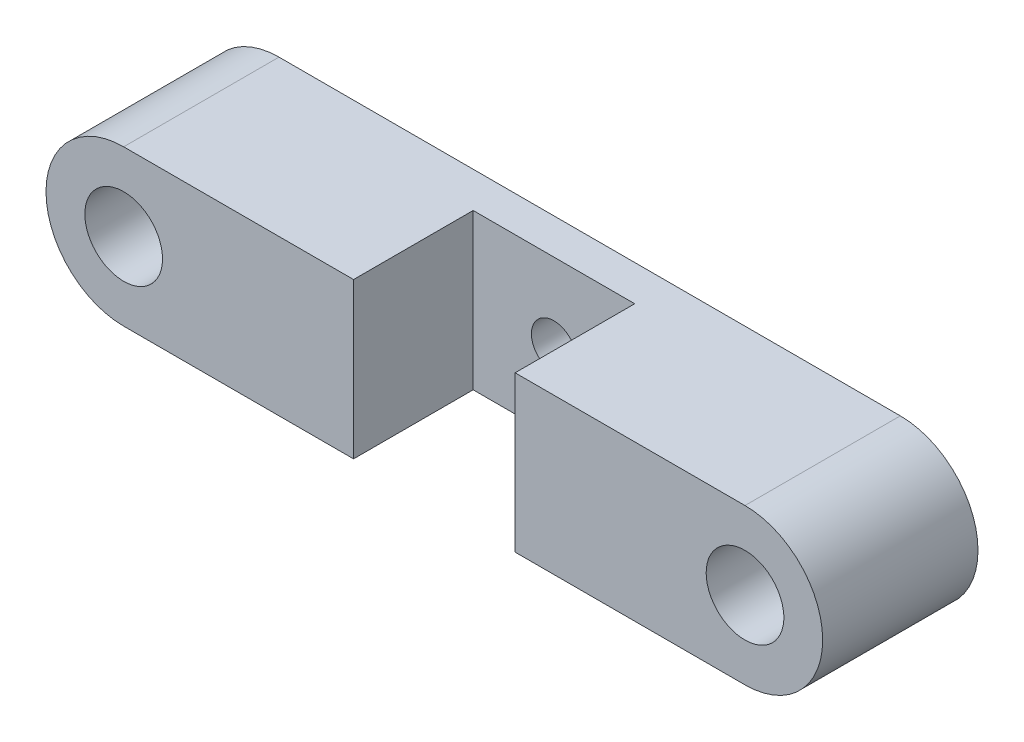
SolidWorks part; units mm, degrees
material "ABS"
ref_plane "Front Plane" through (0, 0, 0) normal (0, 0, 1) x (1, 0, 0)
ref_plane "Top Plane" through (0, 0, 0) normal (0, 1, 0) x (1, 0, 0)
ref_plane "Right Plane" through (0, 0, 0) normal (1, 0, 0) x (0, 0, -1)
sketch "Sketch1" plane through (0, 0, 0) normal (0, 0, 1) x (1, 0, 0)
  line L0 (-50.8, 0) -> (50.8, 0) construction
  line L1 (-50.8, 12.7) -> (50.8, 12.7)
  line L2 (-50.8, -12.7) -> (50.8, -12.7)
  line L3 (0, 34.5997) -> (0, -36.6368) construction
  arc A0 (-50.8, 12.7) -> (-50.8, -12.7) centre (-50.8, 0) ccw
  arc A1 (50.8, -12.7) -> (50.8, 12.7) centre (50.8, 0) ccw
  circle A2 centre (-50.8, 0) radius 6.35
  circle A3 centre (50.8, 0) radius 6.35
  point P3 (0, 0)
  dimension "D3" = 12.7
  dimension "D1" = 101.6
  dimension "D2" = 25.4
extrude "Boss-Extrude1" add sketch "Sketch1" along normal blind 25.4
sketch "Sketch2" plane through (0, 12.7, 0) normal (0, 1, 0) x (1, 0, 0)
  line L0 (50.8, -25.4) -> (-50.8, -25.4) construction
  line L1 (-12.7, -6.35) -> (12.7, -6.35) construction
  line L2 (-12.7, -6.35) -> (-12.7, -44.45) construction
  line L3 (-12.7, -44.45) -> (12.7, -44.45) construction
  line L4 (12.7, -6.35) -> (12.7, -44.45) construction
  line L5 (-12.7, -6.35) -> (12.7, -44.45) construction
  line L6 (-12.7, -44.45) -> (12.7, -6.35) construction
  line L7 (-13.208, -5.842) -> (-13.208, -44.958)
  line L8 (-13.208, -44.958) -> (13.208, -44.958)
  line L9 (13.208, -5.842) -> (13.208, -44.958)
  line L10 (-13.208, -5.842) -> (13.208, -5.842)
  point P0 (0, -25.4)
  dimension "D1" = 38.1
  dimension "D2" = 25.4
  dimension "D3" = 0.508
extrude "Cut-Extrude1" cut sketch "Sketch2" against normal through all
sketch "Sketch3" plane through (0, 0, 5.842) normal (0, 0, 1) x (1, 0, 0)
  circle A0 centre (0, 0) radius 3.175 construction
  circle A1 centre (0, 0) radius 3.683
  dimension "D1" = 6.35
  dimension "D2" = 0.508
extrude "Cut-Extrude2" cut sketch "Sketch3" against normal through all
